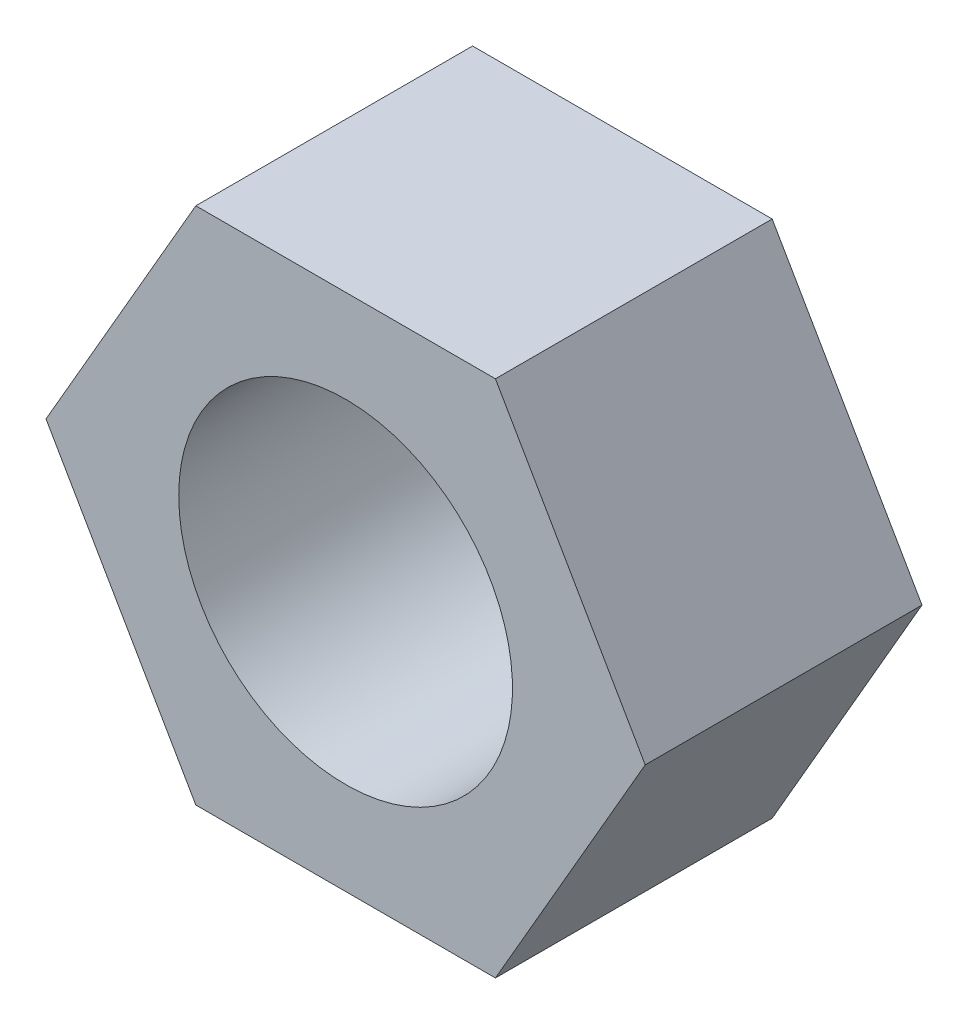
SolidWorks part; units mm, degrees
ref_plane "Front Plane" through (0, 0, 0) normal (0, 0, 1) x (1, 0, 0)
ref_plane "Top Plane" through (0, 0, 0) normal (0, 1, 0) x (1, 0, 0)
ref_plane "Right Plane" through (0, 0, 0) normal (1, 0, 0) x (0, 0, -1)
sketch "Sketch1" plane through (0, 0, 0) normal (0, 0, 1) x (1, 0, 0)
  line L7 (8.6603, -15) -> (17.3205, 0)
  line L8 (17.3205, 0) -> (8.6603, 15)
  line L9 (8.6603, 15) -> (-8.6603, 15)
  line L10 (-8.6603, 15) -> (-17.3205, 0)
  line L11 (-17.3205, 0) -> (-8.6603, -15)
  line L12 (-8.6603, -15) -> (8.6603, -15)
  circle A0 centre (0, 0) radius 15 construction
  dimension "D1" = 30
extrude "Boss-Extrude1" add sketch "Sketch1" along normal blind 16
sketch "Sketch2" plane through (0, 0, 0) normal (0, 0, -1) x (-1, 0, 0)
  circle A0 centre (0, 0) radius 9.647
  dimension "D1" = 19.294
extrude "Cut-Extrude1" cut sketch "Sketch2" against normal blind 16
sketch "Sketch3" plane through (0, 0, 0) normal (0, 0, -1) x (-1, 0, 0)
  circle A0 centre (0, 0) radius 9.188
  dimension "D1" = 18.376
curve "Helix/Spiral2" pitch 2.5 height 17 turns 6.8
sketch "Sketch5" plane through (0, 0, 0) normal (0, 1, 0) x (1, 0, 0)
  line L0 (23.0024, 0) -> (-27.0188, 0) construction
